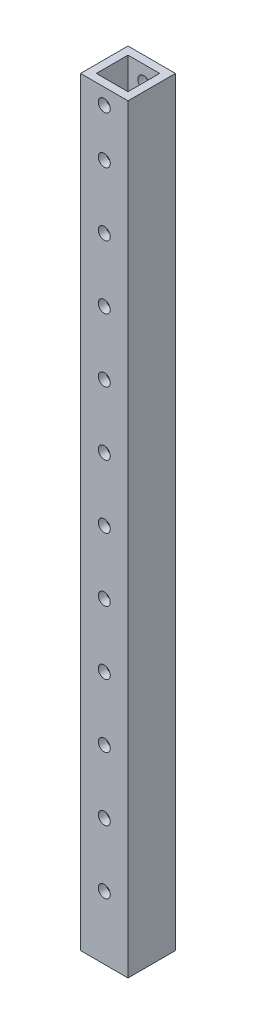
SolidWorks part; units mm, degrees
ref_plane "Front Plane" through (0, 0, 0) normal (0, 0, 1) x (1, 0, 0)
ref_plane "Top Plane" through (0, 0, 0) normal (0, 1, 0) x (1, 0, 0)
ref_plane "Right Plane" through (0, 0, 0) normal (1, 0, 0) x (0, 0, -1)
sketch "Sketch2" plane through (0, 0, 0) normal (0, 1, 0) x (1, 0, 0)
  line L1 (-19.05, -19.05) -> (19.05, -19.05)
  line L2 (-19.05, -19.05) -> (-19.05, 19.05)
  line L3 (-19.05, 19.05) -> (19.05, 19.05)
  line L4 (19.05, -19.05) -> (19.05, 19.05)
  line L5 (-19.05, -19.05) -> (19.05, 19.05) construction
  line L6 (-19.05, 19.05) -> (19.05, -19.05) construction
  line L7 (-12.7, -12.7) -> (12.7, -12.7)
  line L8 (-12.7, -12.7) -> (-12.7, 12.7)
  line L9 (-12.7, 12.7) -> (12.7, 12.7)
  line L10 (12.7, -12.7) -> (12.7, 12.7)
  line L11 (-12.7, -12.7) -> (12.7, 12.7) construction
  line L12 (-12.7, 12.7) -> (12.7, -12.7) construction
  point P0 (0, 0)
  point P6 (0, 0)
  dimension "D1" = 38.1
  dimension "D2" = 38.1
  dimension "D3" = 25.4
  dimension "D4" = 25.4
extrude "Boss-Extrude1" add sketch "Sketch2" along normal blind 609.6
sketch "Sketch3" plane through (0, 0, 19.05) normal (0, 0, 1) x (1, 0, 0)
  line L0 (-19.05, 609.6) -> (19.05, 609.6) construction
  line L1 (-19.05, 609.6) -> (-19.05, 0) construction
  circle A0 centre (0, 596.9) radius 4.826
  circle A1 centre (0, 558.8) radius 4.826
  circle A2 centre (0, 508) radius 4.826
  circle A3 centre (0, 457.2) radius 4.826
  circle A4 centre (0, 406.4) radius 4.826
  circle A5 centre (0, 355.6) radius 4.826
  circle A6 centre (0, 304.8) radius 4.826
  circle A7 centre (0, 254) radius 4.826
  circle A8 centre (0, 203.2) radius 4.826
  circle A9 centre (0, 152.4) radius 4.826
  circle A10 centre (0, 101.6) radius 4.826
  circle A11 centre (0, 50.8) radius 4.826
  dimension "D2" = 9.652
  dimension "D4" = 9.652
  dimension "D1" = 12.7
  dimension "D3" = 19.05
  dimension "D5" = 50.8
  dimension "D6" = 19.05
  dimension "D8" = 50.8
  dimension "D7" = 11
extrude "Cut-Extrude1" cut sketch "Sketch3" against normal blind 609.6 contours A0 | A1 | A2 | A3 | A4 | A5 | A6 | A7 | A8 | A9 | A10 | A11
